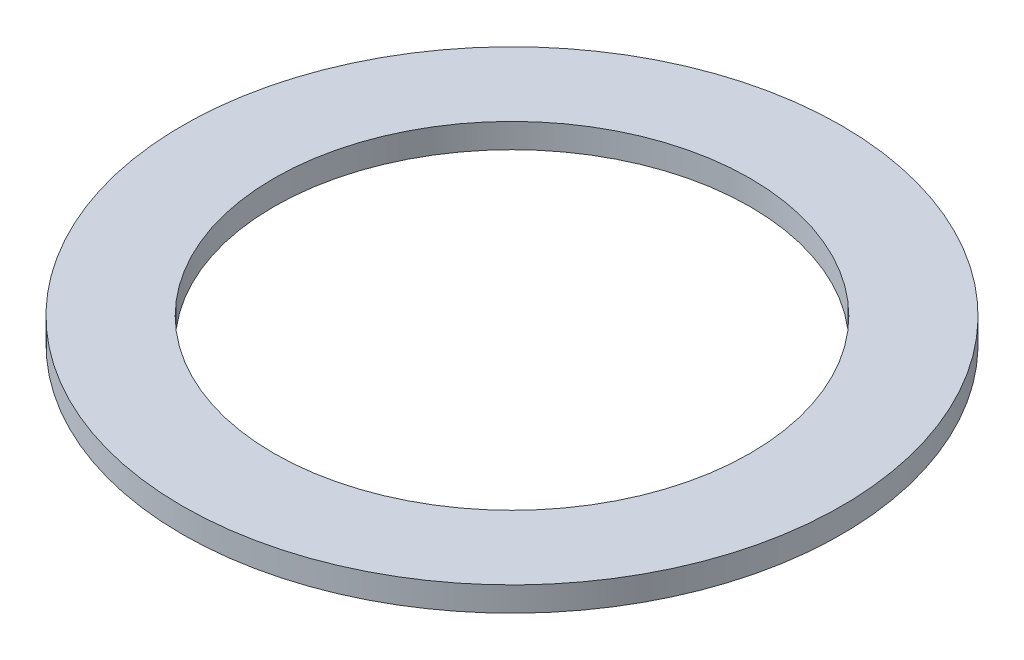
SolidWorks part; units mm, degrees
ref_plane "Front Plane" through (0, 0, 0) normal (0, 0, 1) x (1, 0, 0)
ref_plane "Top Plane" through (0, 0, 0) normal (0, 1, 0) x (1, 0, 0)
ref_plane "Right Plane" through (0, 0, 0) normal (1, 0, 0) x (0, 0, -1)
sketch "Sketch1" plane through (0, 0, 0) normal (0, 0, 1) x (1, 0, 0)
  line L1 (19.4945, 2.0066) -> (26.9748, 2.0066)
  line L2 (19.4945, 2.0066) -> (19.4945, 0)
  line L3 (19.4945, 0) -> (26.9748, 0)
  line L4 (26.9748, 2.0066) -> (26.9748, 0)
  dimension "D1" = 19.4945
  dimension "D2" = 26.9748
  dimension "D3" = 2.0066
ref_axis "central axis" through (0, 0.1952, 0) along (0, 1, 0)
revolve "Revolve1" add sketch "Sketch1" angle 360 about axis through (0, 0.1952, 0) along (0, 1, 0)
